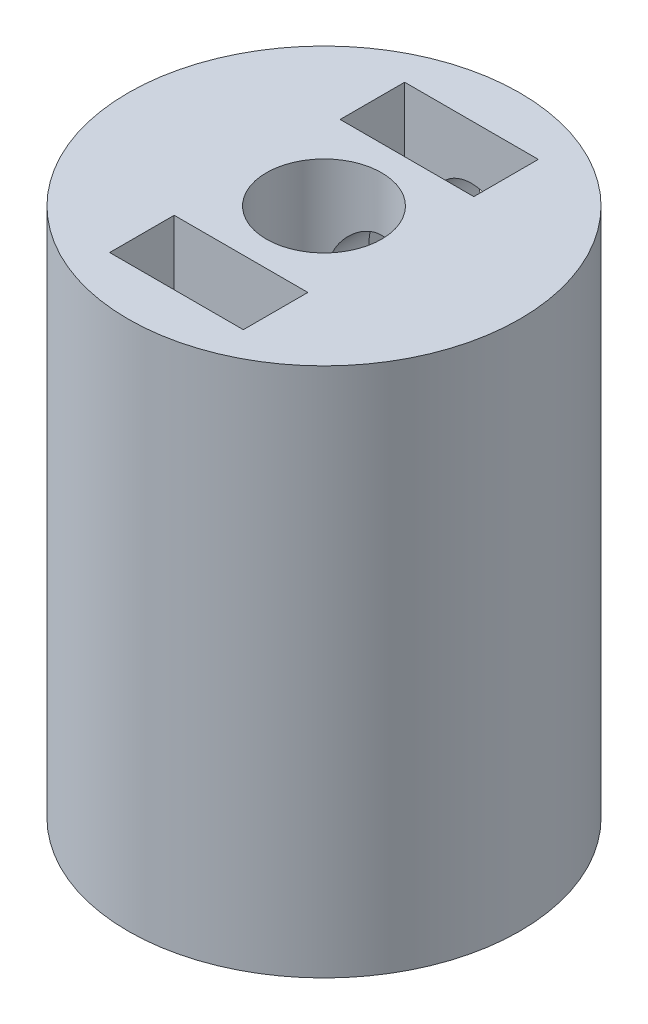
SolidWorks part; units mm, degrees
ref_plane "Front Plane" through (0, 0, 0) normal (0, 0, 1) x (1, 0, 0)
ref_plane "Top Plane" through (0, 0, 0) normal (0, 1, 0) x (1, 0, 0)
ref_plane "Right Plane" through (0, 0, 0) normal (1, 0, 0) x (0, 0, -1)
sketch "Sketch1" plane through (0, 0, 0) normal (0, 1, 0) x (1, 0, 0)
  circle A0 centre (0, 0) radius 8.5
  circle A1 centre (0, 0) radius 2.5
  dimension "D1" = 17
  dimension "D2" = 5
extrude "Boss-Extrude1" add sketch "Sketch1" along normal blind 23
sketch "Sketch3" plane through (0, 23, 0) normal (0, 1, 0) x (1, 0, 0)
  line L1 (-2.9, 6.4) -> (2.9, 6.4)
  line L2 (-2.9, 6.4) -> (-2.9, 3.6)
  line L3 (-2.9, 3.6) -> (2.9, 3.6)
  line L4 (2.9, 6.4) -> (2.9, 3.6)
  line L5 (-2.9, 6.4) -> (2.9, 3.6) construction
  line L6 (-2.9, 3.6) -> (2.9, 6.4) construction
  point P0 (0, 5)
  dimension "D1" = 2.8
  dimension "D2" = 5.8
  dimension "D3" = 5
extrude "Cut-Extrude2" cut sketch "Sketch3" against normal blind 8
sketch "Sketch7" plane through (0, 0, 0) normal (0, -1, 0) x (1, 0, 0)
  line L1 (-2.9, -4.1) -> (2.9, -4.1)
  line L2 (-2.9, -4.1) -> (-2.9, -6.9)
  line L3 (-2.9, -6.9) -> (2.9, -6.9)
  line L4 (2.9, -4.1) -> (2.9, -6.9)
  line L5 (-2.9, -4.1) -> (2.9, -6.9) construction
  line L6 (-2.9, -6.9) -> (2.9, -4.1) construction
  point P0 (0, -5.5)
  dimension "D1" = 2.8
  dimension "D2" = 5.8
  dimension "D3" = 5.5
extrude "Cut-Extrude5" cut sketch "Sketch7" against normal blind 8
sketch "Sketch4" plane through (0, 0, 0) normal (0, 0, 1) x (1, 0, 0)
  line L0 (8.5, 23) -> (-8.5, 23) construction
  circle A0 centre (0, 19) radius 1.65
  circle A1 centre (0, 4) radius 1.65
  dimension "D1" = 3.3
  dimension "D3" = 3.3
  dimension "D2" = 4
  dimension "D4" = 4
extrude "Cut-Extrude3" cut sketch "Sketch4" against normal through all
mirror "Mirror1" about plane through (0, 0, 0) normal (0, 0, 1) of "Cut-Extrude2"
